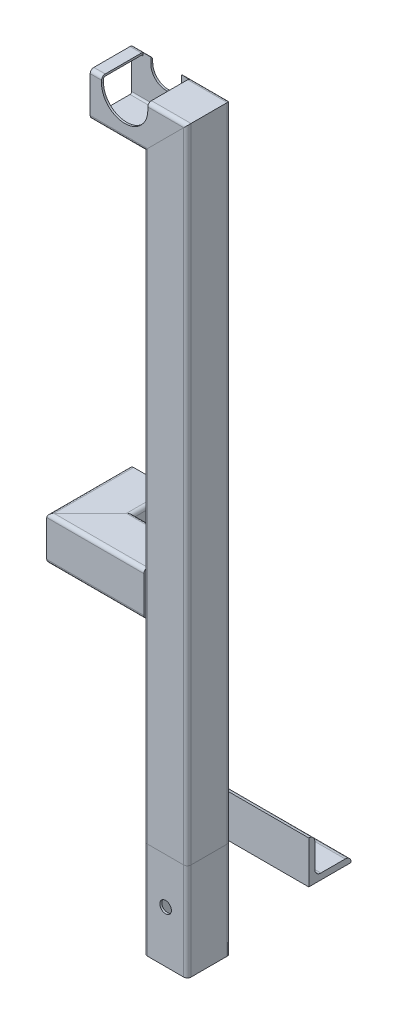
SolidWorks part; units mm, degrees
ref_plane "Front Plane" through (0, 0, 0) normal (0, 0, 1) x (1, 0, 0)
ref_plane "Top Plane" through (0, 0, 0) normal (0, 1, 0) x (1, 0, 0)
ref_plane "Right Plane" through (0, 0, 0) normal (1, 0, 0) x (0, 0, -1)
sketch "Sketch1" plane through (0, 0, 0) normal (0, 0, 1) x (1, 0, 0)
  line L0 (228.7, 0) -> (228.7, 511)
  line L1 (228.7, 511) -> (166.6, 511)
  line L2 (228.7, 0) -> (228.7, -80)
  line L3 (228.7, 176.5) -> (168.7, 176.5)
  dimension "D1" = 511
  dimension "D2" = 80
  dimension "D3" = 62.1
  dimension "D4" = 228.7
  dimension "D5" = 176.5
other "Structural MemberMain"
ref_plane "Plane1" through (228.7, 0, 0) normal (0, 1, 0) x (-1, 0, 0)
sketch "Sketch11" plane through (228.7, 0, 0) normal (0, 1, 0) x (-1, 0, 0)
  line L0 (-14.9, 16.3) -> (14.9, 16.3)
  line L1 (-14.9, 17.9) -> (14.9, 17.9)
  line L2 (-17.9, 14.9) -> (-17.9, -14.9)
  line L3 (-14.9, -17.9) -> (14.9, -17.9)
  line L4 (17.9, 14.9) -> (17.9, -14.9)
  line L5 (-17.9, 17.9) -> (17.9, -17.9) construction
  line L6 (-17.9, -17.9) -> (17.9, 17.9) construction
  line L7 (16.3, 14.9) -> (16.3, -14.9)
  line L8 (-14.9, -16.3) -> (14.9, -16.3)
  line L9 (-16.3, 14.9) -> (-16.3, -14.9)
  arc A0 (-17.9, -14.9) -> (-14.9, -17.9) centre (-14.9, -14.9) ccw
  arc A1 (14.9, -17.9) -> (17.9, -14.9) centre (14.9, -14.9) ccw
  arc A2 (17.9, 14.9) -> (14.9, 17.9) centre (14.9, 14.9) ccw
  arc A3 (-14.9, 17.9) -> (-17.9, 14.9) centre (-14.9, 14.9) ccw
  arc A4 (16.3, 14.9) -> (14.9, 16.3) centre (14.9, 14.9) ccw
  arc A5 (14.9, -16.3) -> (16.3, -14.9) centre (14.9, -14.9) ccw
  arc A6 (-16.3, -14.9) -> (-14.9, -16.3) centre (-14.9, -14.9) ccw
  arc A7 (-14.9, 16.3) -> (-16.3, 14.9) centre (-14.9, 14.9) ccw
  point P0 (0, 0)
  point P30 (0, 0)
  dimension "D3" = 3
  dimension "D1" = 35.8
  dimension "D2" = 35.8
  dimension "D4" = 1.6
sketch "Sketch12" plane through (0, 0, 0) normal (0, 0, 1) x (1, 0, 0)
  line L1 (195, 523.7) -> (195, 534.1) construction
  line L2 (182.3, 523.7) -> (182.3, 534.1)
  line L3 (207.7, 523.7) -> (207.7, 534.1)
  line L4 (228.7, 511) -> (166.6, 511) construction
  line L5 (166.6, 528.9) -> (246.6, 528.9) construction
  arc A0 (182.3, 523.7) -> (207.7, 523.7) centre (195, 523.7) ccw
  arc A1 (207.7, 534.1) -> (182.3, 534.1) centre (195, 534.1) ccw
  point P2 (195, 528.9)
  dimension "D1" = 25.4
  dimension "D2" = 195
extrude "Cut-ExtrudeTopRailGuide" cut sketch "Sketch12" against normal through all and the other way through all
sketch "Sketch13" plane through (0, 0, 0) normal (0, 1, 0) x (1, 0, 0)
  line L0 (210.8, 17.9) -> (310.8, 17.9)
  line L2 (207.7, 17.9) -> (243.6, 17.9) construction
  line L4 (210.8, -14.9) -> (210.8, 14.9) construction
  point P4 (260.8, 17.9)
  dimension "D1" = 100
other "Structural MemberAngle"
ref_plane "Plane2" through (210.8, 0, -17.9) normal (1, 0, 0) x (0, 0, -1)
sketch "Sketch14" plane through (210.8, 0, -17.9) normal (1, 0, 0) x (0, 0, -1)
  line L0 (0, 0) -> (0, 35)
  line L1 (0, 17.5) -> (5, 17.5) construction
  line L2 (5, 30) -> (5, 10)
  line L3 (10, 5) -> (30, 5)
  line L4 (17.5, 5) -> (17.5, 0) construction
  line L5 (35, 0) -> (0, 0)
  arc A0 (35, 0) -> (30, 5) centre (30, 0) ccw
  arc A1 (0, 35) -> (5, 30) centre (0, 30) cw
  arc A2 (10, 5) -> (5, 10) centre (10, 10) cw
  point P10 (17.5, 0)
  point P14 (0, 17.5)
  point P15 (5, 17.5)
  point P16 (17.5, 5)
  point P17 (5, 35)
  point P18 (35, 5)
  point P21 (0, 0)
  dimension "D2" = 5
  dimension "D3" = 35
  dimension "Radius_1" = 5
  dimension "D1" = 5
sketch "Sketch15" plane through (0, 0, 0) normal (0, 1, 0) x (1, 0, 0)
  line L0 (210.8, 17.9) -> (310.8, 17.9) construction
  line L2 (-65.8005, 37.9) -> (459.0005, 37.9) construction
  line L4 (0, 28.933) -> (0, -28.933) construction
  circle A0 centre (179.8, 37.9) radius 4.7625 construction
  circle A1 centre (215.6, 37.9) radius 5.0441 construction
  circle A2 centre (245, 37.9) radius 4.7625
  circle A3 centre (280, 37.9) radius 4.7625
  point P7 (196.6, 37.9)
  point P16 (0, 0)
  dimension "D2" = 9.525
  dimension "D1" = 20
  dimension "D3" = 215.6
  dimension "D4" = 35.8
  dimension "D5" = 35
  dimension "D6" = 280
extrude "Cut-ExtrudeMountingHoles" cut sketch "Sketch15" along normal through all
sketch "Sketch16" plane through (0, 0, 0) normal (0, 0, 1) x (1, 0, 0)
  line L4 (214.05, 523.7) -> (214.05, 534.1)
  line L5 (175.95, 534.1) -> (175.95, 523.7)
  line L6 (214.05, 523.7) -> (214.05, 534.1)
  line L7 (175.95, 534.1) -> (175.95, 523.7)
  arc A4 (175.95, 523.7) -> (214.05, 523.7) centre (195, 523.7) ccw
  arc A5 (214.05, 534.1) -> (175.95, 534.1) centre (195, 534.1) ccw
  arc A6 (175.95, 523.7) -> (214.05, 523.7) centre (195, 523.7) ccw
  arc A7 (214.05, 534.1) -> (175.95, 534.1) centre (195, 534.1) ccw
  dimension "D1" = 6.35
extrude "Cut-ExtrudeEnlargeRailGuide" cut sketch "Sketch16" against normal up to surface and the other way through all
sketch "Sketch17" plane through (0, 0, -17.9) normal (0, 0, -1) x (-1, 0, 0)
  line L0 (-246.6, 510) -> (-166.6, 510)
  line L1 (-246.6, 528.9) -> (-246.6, 0) construction
  line L2 (-166.6, 525.9) -> (-166.6, 496.1) construction
  line L3 (-246.6, 194.4) -> (-168.7, 194.4)
  dimension "D1" = 194.4
  dimension "D2" = 510
ref_plane "Plane4" through (0, 176.5, 0) normal (0, 1, 0) x (-1, 0, 0)
sketch "Sketch20" plane through (0, 176.5, 0) normal (0, 1, 0) x (-1, 0, 0)
  line L0 (-228.7, 0) -> (-148.7, 0)
  line L1 (-228.7, 0) -> (-168.7, 0) construction
  line L2 (-148.7, 0) -> (-148.7, -50.6)
  dimension "D1" = 80
  dimension "D2" = 50.6
other "Structural Member2"
ref_plane "Plane5" through (228.7, 176.5, 0) normal (-1, 0, 0) x (0, 0, 1)
sketch "Sketch110" plane through (228.7, 176.5, 0) normal (-1, 0, 0) x (0, 0, 1)
  line L0 (-14.9, 16.3) -> (14.9, 16.3)
  line L1 (-14.9, 17.9) -> (14.9, 17.9)
  line L2 (-17.9, 14.9) -> (-17.9, -14.9)
  line L3 (-14.9, -17.9) -> (14.9, -17.9)
  line L4 (17.9, 14.9) -> (17.9, -14.9)
  line L5 (-17.9, 17.9) -> (17.9, -17.9) construction
  line L6 (-17.9, -17.9) -> (17.9, 17.9) construction
  line L7 (16.3, 14.9) -> (16.3, -14.9)
  line L8 (-14.9, -16.3) -> (14.9, -16.3)
  line L9 (-16.3, 14.9) -> (-16.3, -14.9)
  arc A0 (-17.9, -14.9) -> (-14.9, -17.9) centre (-14.9, -14.9) ccw
  arc A1 (14.9, -17.9) -> (17.9, -14.9) centre (14.9, -14.9) ccw
  arc A2 (17.9, 14.9) -> (14.9, 17.9) centre (14.9, 14.9) ccw
  arc A3 (-14.9, 17.9) -> (-17.9, 14.9) centre (-14.9, 14.9) ccw
  arc A4 (16.3, 14.9) -> (14.9, 16.3) centre (14.9, 14.9) ccw
  arc A5 (14.9, -16.3) -> (16.3, -14.9) centre (14.9, -14.9) ccw
  arc A6 (-16.3, -14.9) -> (-14.9, -16.3) centre (-14.9, -14.9) ccw
  arc A7 (-14.9, 16.3) -> (-16.3, 14.9) centre (-14.9, 14.9) ccw
  point P0 (0, 0)
  point P30 (0, 0)
  dimension "D3" = 3
  dimension "D1" = 35.8
  dimension "D2" = 35.8
  dimension "D4" = 1.6
other "Trim/Extend1"
sketch "Sketch111" plane through (0, 0, 17.9) normal (0, 0, 1) x (1, 0, 0)
  line L0 (228.7, -37.5) -> (228.7, -80) construction
  line L1 (213.8, -80) -> (243.6, -80) construction
  line L2 (310.8, 0) -> (210.8, 0) construction
  circle A0 centre (228.7, -37.5) radius 4.7625
  dimension "D1" = 9.525
  dimension "D2" = 37.5
extrude "Cut-Extrude1" cut sketch "Sketch111" against normal through all
